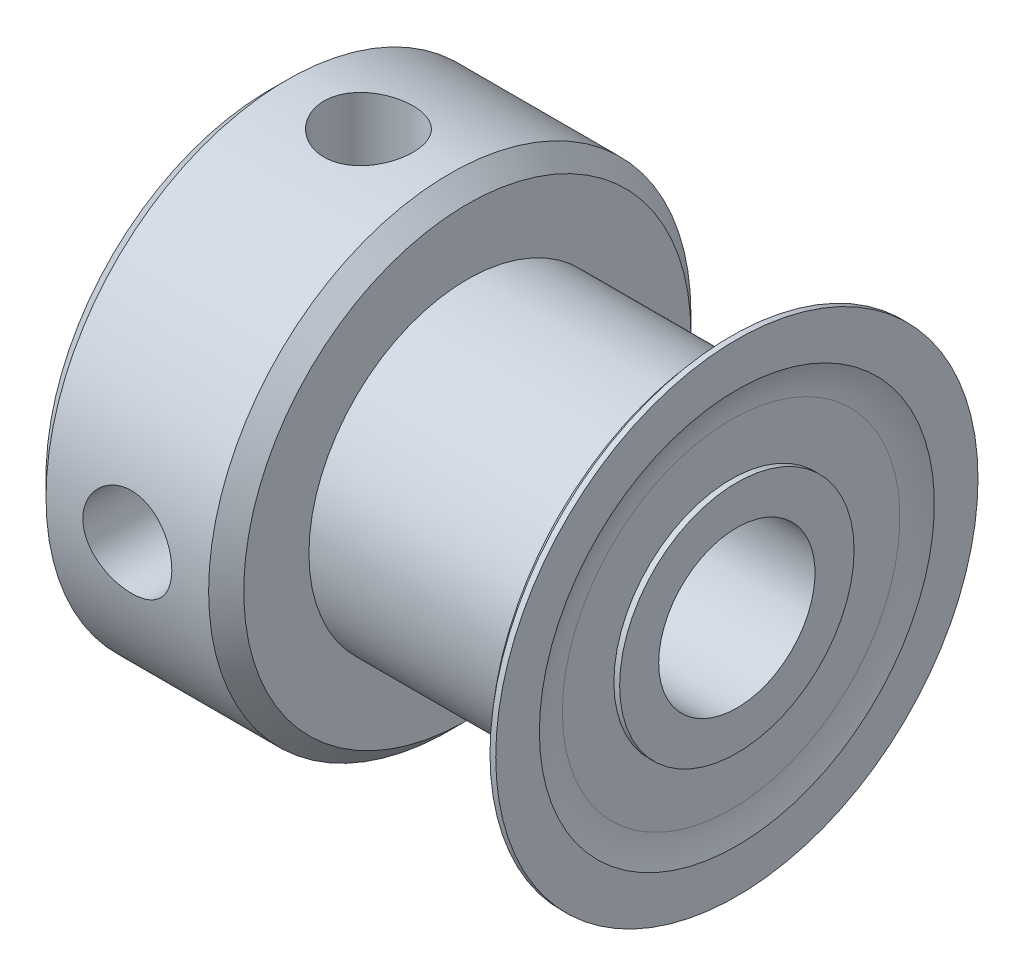
SolidWorks part; units mm, degrees
ref_plane "Front Plane" through (0, 0, 0) normal (0, 0, 1) x (1, 0, 0)
ref_plane "Top Plane" through (0, 0, 0) normal (0, 1, 0) x (1, 0, 0)
ref_plane "Right Plane" through (0, 0, 0) normal (1, 0, 0) x (0, 0, -1)
sketch "Sketch2" plane through (0, 0, 0) normal (0, 0, 1) x (1, 0, 0)
  line L1 (-7.1374, 0) -> (7.1374, 0) construction
  line L2 (0, -1.094) -> (0, 4.8952) construction
  line L3 (-7.1374, 2.3876) -> (7.1374, 2.3876)
  line L4 (-7.1374, 2.3876) -> (-7.1374, 3.5814)
  line L5 (-7.1374, 3.5814) -> (-1.096, 3.5814)
  line L6 (-1.096, 3.5814) -> (-1.096, 4.8387)
  line L7 (-1.096, 4.8387) -> (6.0668, 4.8387)
  line L8 (6.0668, 4.8387) -> (6.0668, 3.5814)
  line L9 (6.0668, 3.5814) -> (7.1374, 3.5814)
  line L10 (7.1374, 3.5814) -> (7.1374, 2.3876)
  dimension "D3" = 1.0706
  dimension "D4" = 7.1628
  dimension "Dimension [E]" = 14.2748
  dimension "Bore [A]" = 4.7752
  dimension "Width [DD]" = 7.1628
  dimension "Outside Diameter [B]" = 9.6774
revolve "Base Body" add sketch "Sketch2" angle 360 about L1
sketch "Sketch3" plane through (0, 0, 0) normal (0, 1, 0) x (1, 0, 0)
  line L0 (-1.096, 3.5814) -> (-7.1374, 3.5814) construction
  line L1 (-1.096, 3.5814) -> (-7.1374, 3.5814)
  line L2 (-1.096, 3.5814) -> (-1.096, 6.8288)
  line L3 (-1.6332, 7.366) -> (-6.6002, 7.366)
  line L4 (-7.1374, 3.5814) -> (-7.1374, 6.8288)
  line L5 (-1.096, 4.8387) -> (-1.096, -4.8387) construction
  line L6 (-7.1374, 6.8288) -> (-6.6002, 7.366)
  line L7 (0, 0) -> (-7.1374, 0) construction
  line L8 (-7.1374, 3.5814) -> (-7.1374, -3.5814) construction
  line L9 (-4.1167, 3.5814) -> (-4.1167, 6.096) construction
  line L10 (-1.096, 6.8288) -> (-1.6332, 7.366)
  line L11 (-7.1374, 6.8288) -> (-7.1374, 7.366) construction
  line L12 (-7.1374, 7.366) -> (-6.6002, 7.366) construction
  dimension "Hub Diameter [F]" = 14.732
  dimension "D2" = 0.5372
revolve "Hub" add sketch "Sketch3" angle 360 about L7
sketch "Sketch4" plane through (0, 0, 0) normal (0, 1, 0) x (1, 0, 0)
  line L0 (6.0668, 3.5814) -> (6.0668, 5.1562)
  line L3 (0, 0) -> (7.0313, 0) construction
  line L4 (6.0668, 3.5814) -> (6.962, 3.5814)
  line L5 (6.962, 3.5814) -> (6.962, 5.1562)
  line L6 (6.962, 7.366) -> (7.1374, 6.0331) construction
  line L7 (6.962, 7.366) -> (7.1374, 7.366)
  line L8 (7.1374, 7.366) -> (7.1374, 6.0331)
  arc A0 (6.0668, 5.1562) -> (6.962, 7.366) centre (9.2418, 5.1562) cw
  arc A1 (6.962, 5.1562) -> (7.1374, 6.0331) centre (9.2418, 5.1562) cw
  dimension "D2" = 3.175
  dimension "D1" = 5.1562
  dimension "Diameter [CC]" = 14.732
revolve "Flange" add sketch "Sketch4" angle 360 about L3
sketch "Sketch5" plane through (0, 0, 0) normal (0, 1, 0) x (1, 0, 0)
  line L0 (-4.1167, 7.366) -> (-4.1167, -7.366) construction
  line L1 (-6.6002, -7.366) -> (-1.6332, -7.366) construction
  line L2 (-1.6332, 7.366) -> (-6.6002, 7.366) construction
  circle A0 centre (-4.1167, 0) radius 1.3589
  dimension "Diameter [DI]" = 2.7178
extrude "Set Screws" cut sketch "Sketch5" along normal blind 10
cosmetic thread "Cosmetic Thread2" parameters "D2"=2.8537
pattern_circular "CirPattern1" count 2 over 90 about axis through (-7.1374, 0, 0) along (1, 0, 0) of "Set Screws"
cosmetic thread "Cosmetic Thread1" parameters "D2"=2.8537
equation "\"D4@Sketch2\" = \"Bore [A]@Sketch2\"*1.5"
equation "\"D3@Sketch2\" = \"Dimension [E]@Sketch2\"*.075"
equation "\"D2@Sketch3\" = \"Width [DD]@Sketch2\"*.075"
equation "\"D1@Sketch4\" = \"Diameter [CC]@Sketch4\"*.35"
equation "\"D2@Cosmetic Thread2\" = \"Diameter [DI]@Sketch5\"*1.05"
equation "\"D2@Cosmetic Thread1\" = \"D2@Cosmetic Thread2\""
